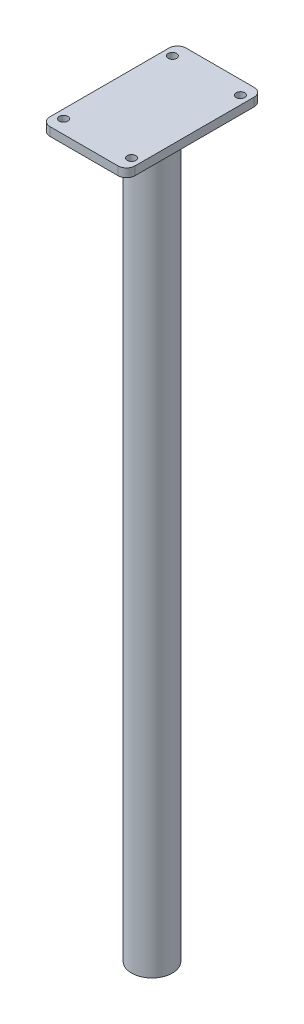
SolidWorks part; units mm, degrees
material "6063-O"
ref_plane "Front Plane" through (0, 0, 0) normal (0, 0, 1) x (1, 0, 0)
ref_plane "Top Plane" through (0, 0, 0) normal (0, 1, 0) x (1, 0, 0)
ref_plane "Right Plane" through (0, 0, 0) normal (1, 0, 0) x (0, 0, -1)
sketch "Sketch1" plane through (0, 0, 0) normal (0, 1, 0) x (1, 0, 0)
  circle A0 centre (0, 0) radius 12
  dimension "D1" = 24
extrude "Boss-Extrude1" add sketch "Sketch1" against normal blind 430
sketch "Sketch2" plane through (0, 0, 0) normal (0, 1, 0) x (1, 0, 0)
  line L1 (-20, 40) -> (20, 40)
  line L2 (-25, 35) -> (-25, -35)
  line L3 (-20, -40) -> (20, -40)
  line L4 (25, 35) -> (25, -35)
  line L5 (-25, 40) -> (25, -40) construction
  line L6 (-25, -40) -> (25, 40) construction
  circle A0 centre (-20, 32) radius 2.5
  circle A1 centre (-20, -32) radius 2.5
  circle A2 centre (20, -32) radius 2.5
  circle A3 centre (20, 32) radius 2.5
  arc A4 (20, -40) -> (25, -35) centre (20, -35) ccw
  arc A5 (-20, -40) -> (-25, -35) centre (-20, -35) cw
  arc A6 (20, 40) -> (25, 35) centre (20, 35) cw
  arc A7 (-20, 40) -> (-25, 35) centre (-20, 35) ccw
  point P0 (0, 0)
  dimension "D1" = 5
  dimension "D5" = 5
  dimension "D6" = 5
  dimension "D7" = 5
  dimension "D8" = 5
  dimension "D2" = 80
  dimension "D3" = 50
  dimension "D4" = 40
extrude "Boss-Extrude2" add sketch "Sketch2" along normal blind 5
sketch "Sketch3" plane through (0, -430, 0) normal (0, -1, 0) x (1, 0, 0)
  circle A0 centre (0, 0) radius 5
  dimension "D1" = 10
extrude "Cut-Extrude1" cut sketch "Sketch3" against normal blind 50
